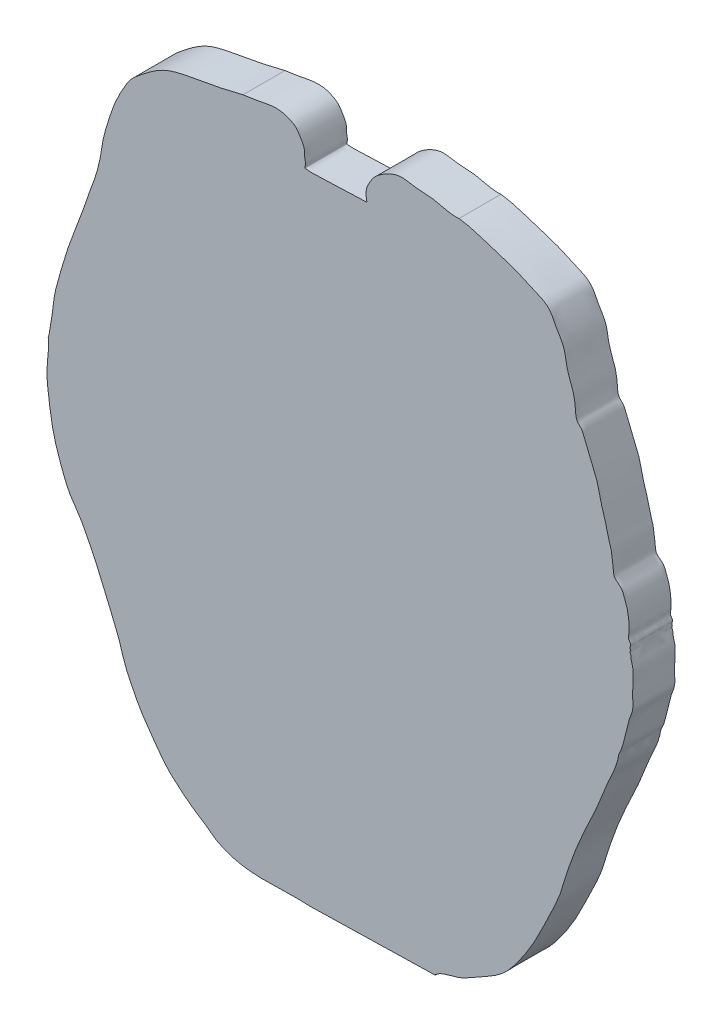
SolidWorks part; units mm, degrees
ref_plane "Front Plane" through (0, 0, 0) normal (0, 0, 1) x (1, 0, 0)
ref_plane "Top Plane" through (0, 0, 0) normal (0, 1, 0) x (1, 0, 0)
ref_plane "Right Plane" through (0, 0, 0) normal (1, 0, 0) x (0, 0, -1)
sketch "faceplate" plane through (0, 0, 0) normal (0, 0, 1) x (1, 0, 0)
  line L0 (-773.8445, -610.7592) -> (-773.8445, -482.7592) construction
  line L2 (-544.9945, -612.5151) -> (-544.9945, -613.5151)
  line L3 (-544.9945, -613.5151) -> (-843.9945, -620.5151)
  line L7 (-523.9945, 980.4849) -> (-523.9945, 979.4849)
  circle A0 centre (-1073.4896, 48.4342) radius 1.2806
  spline S0 degree 3 poles (-709.9945, 914.4849) (-710.0251, 928.1113) (-706.5565, 936.4698) (-693.3579, 960.7099) (-674.7112, 975.8825) (-653.0691, 988.2724) (-626.3616, 997.1524) (-592.8389, 988.512) (-545.4591, 990.0156) (-510.6759, 975.2889) (-488.1743, 977.7041) knots 0 0 0 0 0.092656 0.18325 0.277762 0.36801 0.465335 0.586986 0.74978 1 1 1 1
  spline S1 degree 3 poles (-1067.8024, -595.3231) (-997.1183, -634.9808) (-919.0071, -615.3883) (-843.9945, -620.5151) knots 0 0 0 0 1 1 1 1
  spline S2 degree 3 poles (-488.1743, 977.7041) (-456.2767, 973.7728) (-413.0821, 956.0014) (-352.8805, 940.043) (-315.6704, 920.0968) (-282.6385, 909.1157) (-266.1033, 889.1581) (-255.6269, 864.8305) (-234.9067, 837.4889) (-232.9122, 797.596) (-216.8051, 762.6452) (-210.0517, 729.6559) (-210.4868, 699.6504) (-195.4734, 689.8708) (-190.3569, 675.5693) (-183.2362, 660.1132) (-175.6707, 641.0695) (-169.3011, 624.9443) (-160.9408, 606.9185) (-155.2202, 586.955) (-150.7715, 563.5207) (-144.5263, 542.9589) (-137.3224, 520.6883) (-133.4924, 498.0724) (-124.1682, 475.4951) (-123.5934, 456.0078) (-119.6002, 438.3158) (-120.6777, 423.1131) (-108.9638, 414.0771) (-99.4283, 406.7583) (-95.0923, 394.9591) (-90.6927, 383.6733) (-86.968, 372.6448) (-85.0294, 361.0894) (-83.0676, 348.9606) (-83.1328, 337.6461) (-81.4047, 324.462) (-87.1355, 311.9677) (-77.0075, 302.8965) (-81.4512, 296.34) (-78.9923, 290.9126) (-81.1248, 285.3827) (-77.851, 280.395) (-78.2828, 272.5389) (-75.6949, 264.1427) (-72.8991, 253.1366) (-73.3456, 242.4376) (-72.9361, 230.5192) (-74.2579, 218.8955) (-73.6736, 207.2321) (-74.8004, 194.0668) (-72.6711, 179.4446) (-75.2936, 163.0507) (-81.8809, 149.1763) (-87.2229, 126.0974) (-93.8043, 101.1371) (-100.0613, 75.1626) (-107.8827, 61.8619) (-108.7971, 51.7138) (-111.5187, 42.3424) (-115.228, 30.3906) (-120.9282, 16.5564) (-131.7045, -4.9559) (-143.4384, -34.3117) (-156.5135, -68.9344) (-182.1565, -121.8324) (-208.6668, -180.1821) (-232.2439, -246.7856) (-247.2852, -303.4044) (-277.4121, -362.6778) (-308.2935, -429.7253) (-344.8457, -485.4058) (-387.3162, -537.8993) (-439.7817, -562.9087) (-491.4334, -596.2005) (-528.7786, -598.006) (-544.9945, -612.5151) knots 0 0 0 0 0.048757 0.071774 0.095128 0.113854 0.123638 0.133836 0.15463 0.174656 0.193345 0.212906 0.227665 0.234662 0.238296 0.250641 0.260992 0.26973 0.277296 0.2915 0.301482 0.31395 0.324487 0.337428 0.349074 0.361675 0.366816 0.377336 0.382347 0.38858 0.395601 0.401012 0.407351 0.413396 0.419001 0.426213 0.430694 0.439509 0.444218 0.447375 0.44963 0.452774 0.455623 0.458079 0.464619 0.469003 0.475464 0.480927 0.487344 0.493373 0.49884 0.507587 0.515914 0.523899 0.531062 0.552209 0.563671 0.572003 0.575322 0.579188 0.586976 0.594554 0.602148 0.623945 0.643093 0.659 0.714253 0.741477 0.767542 0.80402 0.843271 0.880836 0.906434 0.945574 0.968647 1 1 1 1
  spline S3 degree 3 poles (-1003.3213, 975.577) (-987.6253, 977.2529) (-962.7043, 982.1534) (-930.108, 988.2866) (-907.7334, 986.8472) (-890.5067, 980.1538) (-877.2281, 972.8822) (-868.6577, 960.201) (-862.568, 949.919) (-857.6503, 940.262) (-856.6505, 932.1132) (-856.8584, 925.8924) (-856.4841, 920.0511) (-854.9996, 913.5768) (-853.8052, 906.7716) (-856.8918, 896.1799) (-849.5329, 897.8005) (-844.3012, 896.0989) (-836.0513, 896.6642) (-824.3827, 897.3561) (-811.0916, 897.399) (-771.6586, 898.712) (-737.5661, 900.2311) (-707.9614, 901.3525) knots 0 0 0 0 0.132408 0.21369 0.278435 0.316912 0.369103 0.401753 0.443732 0.470308 0.491739 0.511855 0.522604 0.541062 0.565962 0.58919 0.600387 0.616596 0.637288 0.668004 0.715727 0.748605 1 1 1 1
  spline S5 degree 1 poles (-709.9945, 914.4849) (-707.9614, 901.3525) knots 0 0 1 1
  spline S10 degree 3 poles (-1067.8024, -595.3231) (-1086.847, -579.73) (-1119.9702, -561.2241) (-1156.0347, -531.3608) (-1179.1382, -511.2217) (-1196.316, -490.9616) (-1213.2174, -467.461) (-1232.3976, -440.8997) (-1252.4432, -410.6757) (-1269.1726, -376.573) (-1286.5145, -341.0871) (-1296.7387, -301.2324) (-1313.4559, -261.1432) (-1331.0418, -218.7389) (-1349.7104, -174.6284) (-1370.427, -132.1662) (-1390.7016, -90.5738) (-1419.1354, -54.8159) (-1435.3705, -11.4701) (-1451.7684, 32.5025) (-1461.4646, 79.0974) (-1467.2405, 123.638) (-1472.3849, 165.2992) (-1468.8274, 202.6268) (-1466.138, 228.4293) (-1468.2676, 242.7999) (-1465.754, 248.1509) (-1464.4138, 264.201) (-1457.6152, 293.6195) (-1454.3976, 337.8456) (-1438.8759, 390.7488) (-1421.1923, 453.4594) (-1394.5937, 518.9042) (-1375.9228, 572.2311) (-1364.0697, 607.9048) (-1355.2184, 628.9325) (-1349.1781, 652.608) (-1341.6524, 681.8277) (-1338.2166, 716.5654) (-1327.9856, 750.1068) (-1318.018, 782.6162) (-1306.488, 813.1786) (-1292.8354, 838.7097) (-1281.1863, 860.5849) (-1266.2143, 880.0554) (-1236.1395, 903.5659) (-1193.1928, 937.0541) (-1128.9869, 949.724) (-1077.5953, 959.0238) (-1036.0178, 967.0359) (-1015.1349, 973.2005) (-1003.3213, 975.577) knots 0 0 0 0 0.038401 0.058896 0.073102 0.086227 0.100288 0.118345 0.137451 0.156852 0.177685 0.198987 0.220891 0.245489 0.270769 0.29571 0.319371 0.342894 0.366424 0.391142 0.416291 0.440511 0.461426 0.481689 0.49863 0.502577 0.503311 0.507792 0.527347 0.550723 0.576659 0.613251 0.652562 0.686915 0.701565 0.711304 0.72251 0.739688 0.758424 0.776832 0.794317 0.811622 0.827753 0.839523 0.850339 0.865807 0.89907 0.933921 0.965999 0.981185 1 1 1 1
extrude "Boss-Extrude1" add sketch "faceplate" along normal blind 100 contours S10 S3 S5 S0 S2 L2 L3 S1
sketch3d "3DSketch1"
  spline S0 degree 3 poles (-488.1743, 977.7041, 100) (-456.2767, 973.7728, 100) (-413.0821, 956.0014, 100) (-352.8805, 940.043, 100) (-315.6704, 920.0968, 100) (-282.6385, 909.1157, 100) (-266.1033, 889.1581, 100) (-255.6269, 864.8305, 100) (-234.9067, 837.4889, 100) (-232.9122, 797.596, 100) (-216.8051, 762.6452, 100) (-210.0517, 729.6559, 100) (-210.4868, 699.6504, 100) (-195.4734, 689.8708, 100) (-190.3569, 675.5693, 100) (-183.2362, 660.1132, 100) (-175.6707, 641.0695, 100) (-169.3011, 624.9443, 100) (-160.9408, 606.9185, 100) (-155.2202, 586.955, 100) (-150.7715, 563.5207, 100) (-144.5263, 542.9589, 100) (-137.3224, 520.6883, 100) (-133.4924, 498.0724, 100) (-124.1682, 475.4951, 100) (-123.5934, 456.0078, 100) (-119.6002, 438.3158, 100) (-120.6777, 423.1131, 100) (-108.9638, 414.0771, 100) (-99.4283, 406.7583, 100) (-95.0923, 394.9591, 100) (-90.6927, 383.6733, 100) (-86.968, 372.6448, 100) (-85.0294, 361.0894, 100) (-83.0676, 348.9606, 100) (-83.1328, 337.6461, 100) (-81.4047, 324.462, 100) (-87.1355, 311.9677, 100) (-77.0075, 302.8965, 100) (-81.4512, 296.34, 100) (-78.9923, 290.9126, 100) (-81.1248, 285.3827, 100) (-77.851, 280.395, 100) (-78.2828, 272.5389, 100) (-75.6949, 264.1427, 100) (-72.8991, 253.1366, 100) (-73.3456, 242.4376, 100) (-72.9361, 230.5192, 100) (-74.2579, 218.8955, 100) (-73.6736, 207.2321, 100) (-74.8004, 194.0668, 100) (-72.6711, 179.4446, 100) (-75.2936, 163.0507, 100) (-81.8809, 149.1763, 100) (-87.2229, 126.0974, 100) (-93.8043, 101.1371, 100) (-100.0613, 75.1626, 100) (-107.8827, 61.8619, 100) (-108.7971, 51.7138, 100) (-111.5187, 42.3424, 100) (-115.228, 30.3906, 100) (-120.9282, 16.5564, 100) (-131.7045, -4.9559, 100) (-143.4384, -34.3117, 100) (-156.5135, -68.9344, 100) (-182.1565, -121.8324, 100) (-208.6668, -180.1821, 100) (-232.2439, -246.7856, 100) (-247.2852, -303.4044, 100) (-277.4121, -362.6778, 100) (-308.2935, -429.7253, 100) (-344.8457, -485.4058, 100) (-387.3162, -537.8993, 100) (-439.7817, -562.9087, 100) (-491.4334, -596.2005, 100) (-528.7786, -598.006, 100) (-544.9945, -612.5151, 100) knots 0 0 0 0 0.048757 0.071774 0.095128 0.113854 0.123638 0.133836 0.15463 0.174656 0.193345 0.212906 0.227665 0.234662 0.238296 0.250641 0.260992 0.26973 0.277296 0.2915 0.301482 0.31395 0.324487 0.337428 0.349074 0.361675 0.366816 0.377336 0.382347 0.38858 0.395601 0.401012 0.407351 0.413396 0.419001 0.426213 0.430694 0.439509 0.444218 0.447375 0.44963 0.452774 0.455623 0.458079 0.464619 0.469003 0.475464 0.480927 0.487344 0.493373 0.49884 0.507587 0.515914 0.523899 0.531062 0.552209 0.563671 0.572003 0.575322 0.579188 0.586976 0.594554 0.602148 0.623945 0.643093 0.659 0.714253 0.741477 0.767542 0.80402 0.843271 0.880836 0.906434 0.945574 0.968647 1 1 1 1 construction
  point P0 (-204.7037, 697.6312, 100)
